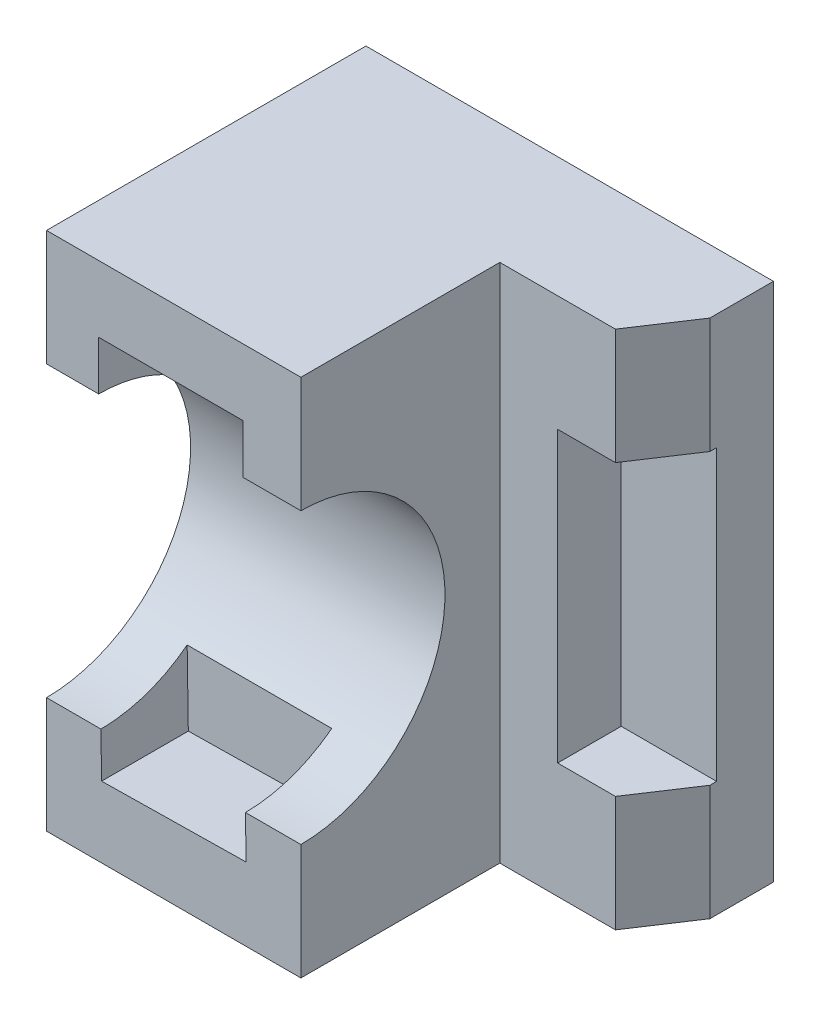
SolidWorks part; units mm, degrees
ref_plane "Front Plane" through (0, 0, 0) normal (0, 0, 1) x (1, 0, 0)
ref_plane "Top Plane" through (0, 0, 0) normal (0, 1, 0) x (1, 0, 0)
ref_plane "Right Plane" through (0, 0, 0) normal (1, 0, 0) x (0, 0, -1)
sketch "Sketch2" plane through (0, 0, 0) normal (0, 0, 1) x (1, 0, 0)
  line L0 (-41.6737, 0) -> (52.8349, 0) construction
  line L2 (-35.25, 45) -> (35.25, 45)
  line L3 (-35.25, 45) -> (-35.25, -45)
  line L4 (-35.25, -45) -> (35.25, -45)
  line L5 (35.25, 45) -> (35.25, -45)
  line L6 (-35.25, 45) -> (35.25, -45) construction
  line L7 (-35.25, -45) -> (35.25, 45) construction
  point P3 (0, 0)
  dimension "D1" = 70.5
  dimension "D2" = 90
extrude "Boss-Extrude1" add sketch "Sketch2" along normal blind 55.25
sketch "Sketch3" plane through (0, -45, 0) normal (0, -1, 0) x (1, 0, 0)
  line L1 (-35.25, 55.25) -> (35.25, 55.25) construction
  line L2 (0, 0) -> (35.25, 0)
  line L3 (35.25, 0) -> (35.25, 11)
  line L4 (35.25, 55.25) -> (35.25, 0) construction
  line L5 (35.25, 11) -> (28.75, 20.8353)
  line L6 (28.75, 20.8353) -> (8.75, 20.8353)
  line L7 (8.75, 20.8353) -> (8.75, 55.25)
  line L9 (-35.25, 55.25) -> (-35.25, 0) construction
  line L10 (8.75, 55.25) -> (35.25, 55.25)
  line L11 (35.25, 55.25) -> (35.25, 11)
  line L12 (-35.25, 0) -> (35.25, 0) construction
  line M9 (35.25, 0) -> (35.25, 55.25)
  line M10 (35.25, 55.25) -> (-35.25, 55.25)
  dimension "D1" = 11
  dimension "D2" = 44
  dimension "D3" = 20
  dimension "D4" = 70.5
  dimension "D5" = 20.8353
extrude "Cut-Extrude1" cut sketch "Sketch3" against normal through all contours L7 L6 L5 M9 M10
sketch "Sketch4" plane through (8.75, 0, 0) normal (1, 0, 0) x (0, 0, -1)
  line L0 (-95.7935, 0) -> (32.4213, 0) construction
  line L2 (-20.8353, 45) -> (-20.8353, -45) construction
  circle A0 centre (-55.3275, 0) radius 25
  dimension "D1" = 50
  dimension "D2" = 34.4923
extrude "Cut-Extrude2" cut sketch "Sketch4" against normal through all
sketch "Sketch6" plane through (0, 0, 20.8353) normal (0, 0, 1) x (1, 0, 0)
  line L0 (-57.5423, 0) -> (70.6785, 0) construction
  line L1 (35.25, 45) -> (35.25, -45) construction
  line L2 (18.75, 25) -> (35.25, 25)
  line L3 (18.75, 25) -> (18.75, -25)
  line L4 (18.75, -25) -> (35.25, -25)
  line L5 (35.25, 25) -> (35.25, -25)
  line L6 (18.75, 25) -> (35.25, -25) construction
  line L7 (18.75, -25) -> (35.25, 25) construction
  point P3 (27, 0)
  dimension "D1" = 16.5
  dimension "D2" = 50
extrude "Cut-Extrude3" cut sketch "Sketch6" against normal blind 11 and the other way through all
sketch "Sketch7" plane through (0, 0, 55.25) normal (0, 0, 1) x (1, 0, 0)
  line L0 (-74.8806, 0) -> (52.34, 0.977) construction
  line L1 (8.75, 45) -> (-35.25, 45) construction
  line L2 (-26.2337, 33.5) -> (-1.2337, 33.5)
  line L3 (-26.2337, 33.5) -> (-26.2337, 18.5)
  line L4 (-26.2337, 18.5) -> (-1.2337, 18.5)
  line L5 (-1.2337, 33.5) -> (-1.2337, 18.5)
  line L6 (-26.2337, 33.5) -> (-1.2337, 18.5) construction
  line L7 (-26.2337, 18.5) -> (-1.2337, 33.5) construction
  line L8 (-25.9553, -17.7507) -> (-0.9583, -17.3668)
  line L9 (-0.7279, -32.365) -> (-0.9583, -17.3668)
  line L10 (-25.7249, -32.7489) -> (-0.7279, -32.365)
  line L11 (-25.7249, -32.7489) -> (-25.9553, -17.7507)
  line L12 (8.75, 45) -> (8.75, 24.9999) construction
  point P2 (-13.7337, 26)
  dimension "D1" = 25
  dimension "D2" = 15
  dimension "D3" = 11.5
  dimension "D4" = 9.4779
  dimension "D5" = 9.7083
  dimension "D6" = 9.9837
extrude "Cut-Extrude4" cut sketch "Sketch7" against normal blind 15
